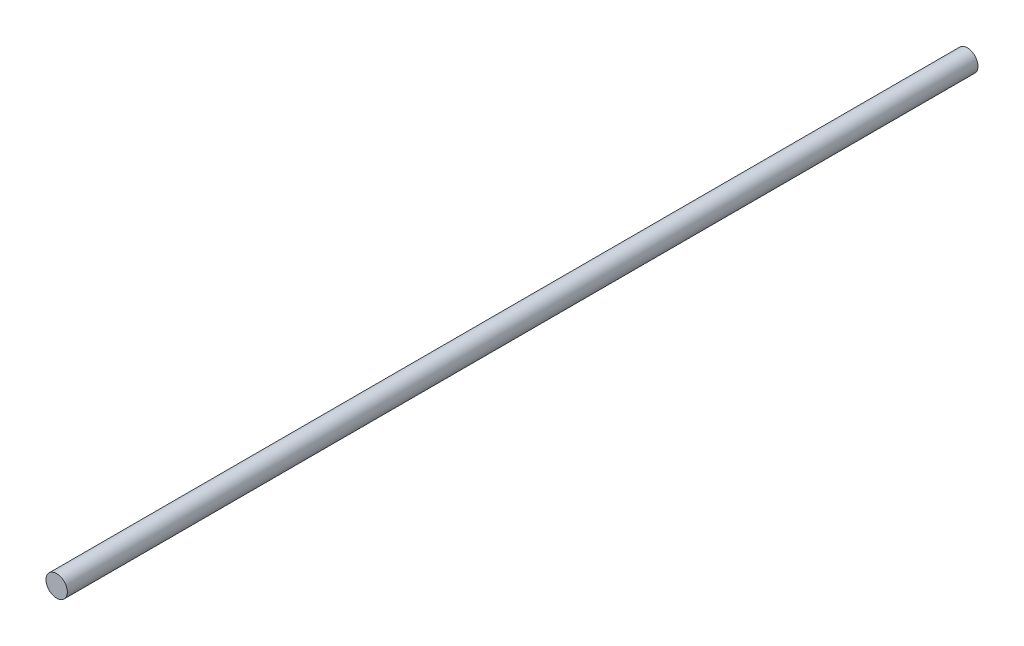
SolidWorks part; units mm, degrees
ref_plane "Front Plane" through (0, 0, 0) normal (0, 0, 1) x (1, 0, 0)
ref_plane "Top Plane" through (0, 0, 0) normal (0, 1, 0) x (1, 0, 0)
ref_plane "Right Plane" through (0, 0, 0) normal (1, 0, 0) x (0, 0, -1)
sketch "Sketch1" plane through (0, 0, 0) normal (0, 0, 1) x (1, 0, 0)
  circle A0 centre (0, 0) radius 2.3813
  dimension "D1" = 4.7625
extrude "Boss-Extrude1" add sketch "Sketch1" along normal blind 203.2
